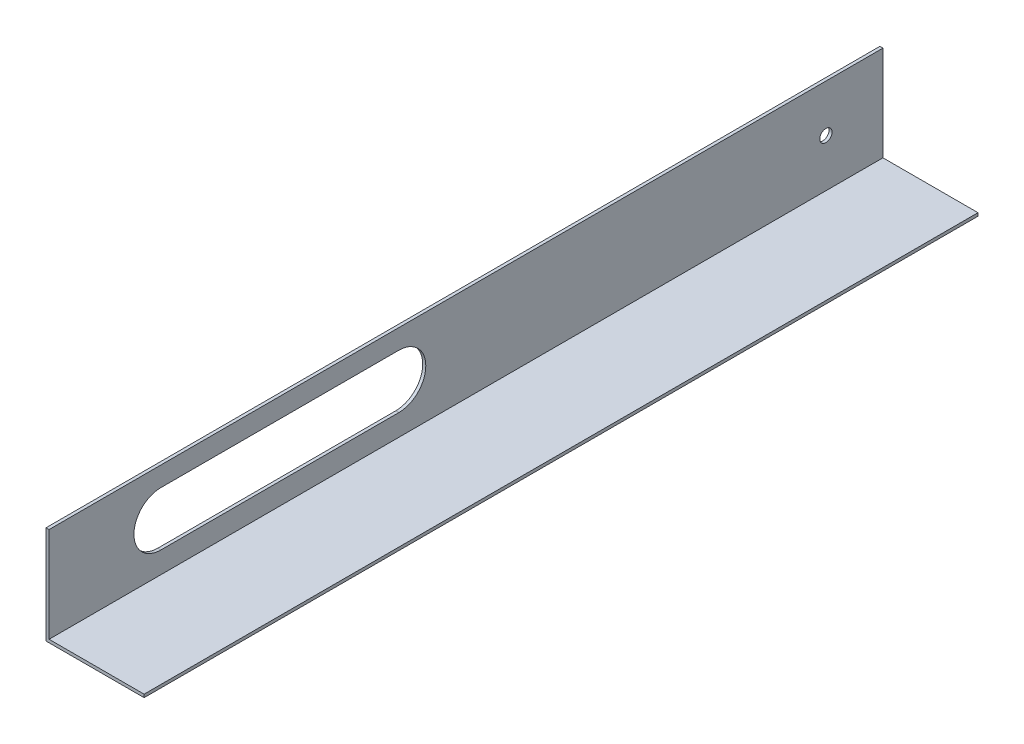
SolidWorks part; units mm, degrees
ref_plane "Front Plane" through (0, 0, 0) normal (0, 0, 1) x (1, 0, 0)
ref_plane "Top Plane" through (0, 0, 0) normal (0, 1, 0) x (1, 0, 0)
ref_plane "Right Plane" through (0, 0, 0) normal (1, 0, 0) x (0, 0, -1)
sketch "Sketch3" plane through (0, 0, 0) normal (0, 0, 1) x (1, 0, 0)
  line L0 (0, 0) -> (0, 49.2125)
  line L1 (0, 49.2125) -> (-1.5875, 49.2125)
  line L2 (-1.5875, 49.2125) -> (-1.5875, -1.5875)
  line L3 (-1.5875, -1.5875) -> (49.2125, -1.5875)
  line L4 (49.2125, -1.5875) -> (49.2125, 0)
  line L5 (49.2125, 0) -> (0, 0)
  dimension "D1" = 1.5875
  dimension "D2" = 1.5875
  dimension "D3" = 50.8
  dimension "D4" = 50.8
extrude "Boss-Extrude2" add sketch "Sketch3" along normal blind 431.8
sketch "Sketch6" plane through (0, 0, 0) normal (1, 0, 0) x (0, 0, -1)
  line L0 (-373.888, 25.0825) -> (-250.698, 25.0825) construction
  line L1 (-373.888, 39.0525) -> (-250.698, 39.0525)
  line L2 (-373.888, 11.1125) -> (-250.698, 11.1125)
  line L3 (-431.8, 0) -> (-431.8, 49.2125) construction
  line L4 (-431.8, 49.2125) -> (0, 49.2125) construction
  line L5 (-431.8, 0) -> (0, 0) construction
  arc A0 (-373.888, 39.0525) -> (-373.888, 11.1125) centre (-373.888, 25.0825) ccw
  arc A1 (-250.698, 11.1125) -> (-250.698, 39.0525) centre (-250.698, 25.0825) ccw
  point P2 (-312.293, 25.0825)
  dimension "D1" = 11.1125
  dimension "D2" = 123.19
  dimension "D3" = 57.912
  dimension "D4" = 24.13
extrude "Cut-Extrude3" cut sketch "Sketch6" against normal blind 127
sketch "Sketch7" plane through (0, 0, 0) normal (1, 0, 0) x (0, 0, -1)
  circle A0 centre (-29.5388, 24.7736) radius 3.175
  dimension "D1" = 6.35
extrude "Cut-Extrude4" cut sketch "Sketch7" against normal blind 127
